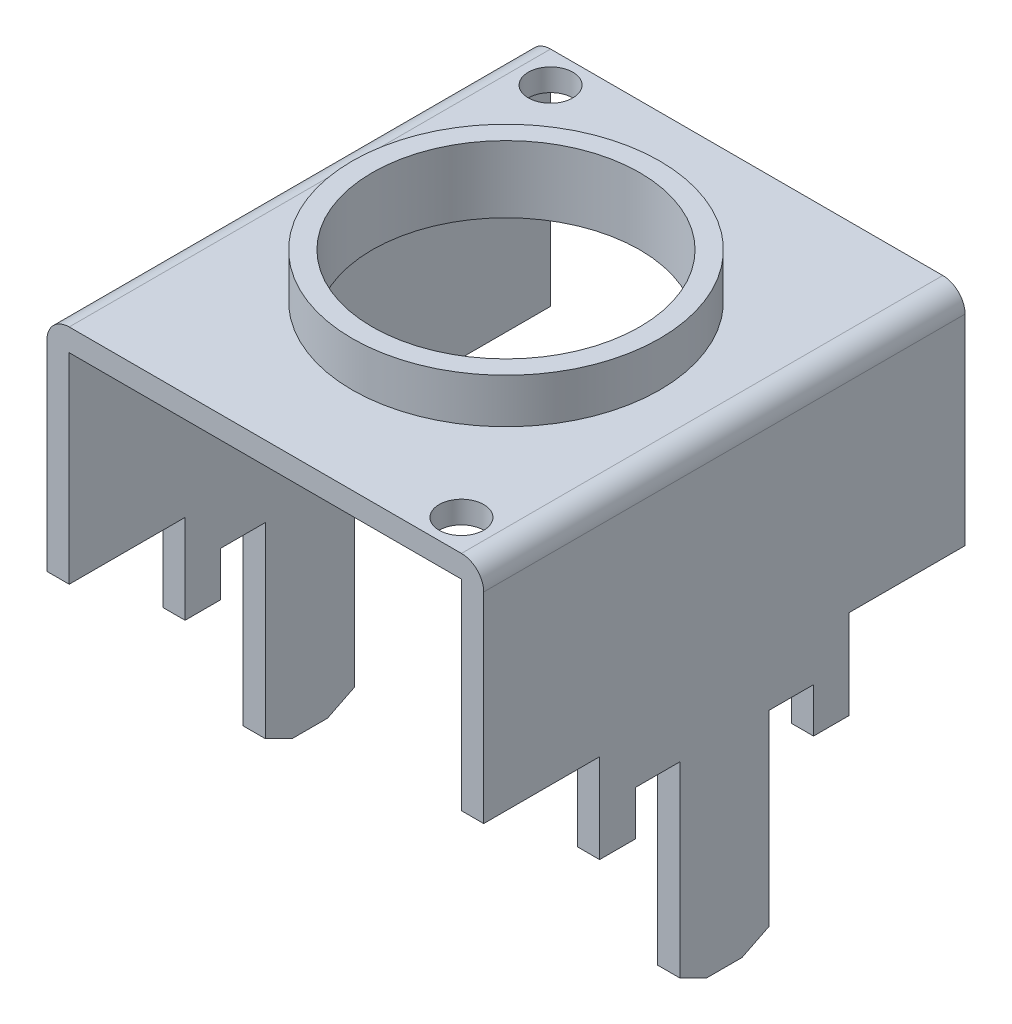
SolidWorks part; units mm, degrees
ref_plane "Plan de face" through (0, 0, 0) normal (0, 0, 1) x (1, 0, 0)
ref_plane "Plan de dessus" through (0, 0, 0) normal (0, 1, 0) x (1, 0, 0)
ref_plane "Plan de droite" through (0, 0, 0) normal (1, 0, 0) x (0, 0, -1)
sketch "Esquisse1" plane through (0, 0, 0) normal (0, 0, 1) x (1, 0, 0)
  line L0 (0, 5.7355) -> (0, -4.9955) construction
  line L1 (-4.9, -3.5) -> (-4.9, 6.5)
  line L2 (-4.4, 7) -> (4.4, 7)
  line L3 (4.9, 6.5) -> (4.9, -3.5)
  arc A0 (4.4, 7) -> (4.9, 6.5) centre (4.4, 6.5) cw
  arc A1 (-4.9, 6.5) -> (-4.4, 7) centre (-4.4, 6.5) cw
  dimension "D4" = 0.5
  dimension "D1" = 9.8
  dimension "D2" = 7
  dimension "D3" = 3.5
extrude "Extru.-Mince1" add sketch "Esquisse1" along normal blind 5.4 and the other way blind 5.4 thin
sketch "Esquisse3" plane through (0, 0, 0) normal (1, 0, 0) x (0, 0, -1)
  line L0 (0, 8.2867) -> (0, -5.5025) construction
  line L1 (-6.3578, 0) -> (5.9157, 0) construction
  line L2 (-6, 2) -> (-2.8, 2)
  line L3 (-2.8, 2) -> (-2.8, 0)
  line L4 (-2.8, 0) -> (-2, 0)
  line L5 (-2, 0) -> (-2, 1)
  line L6 (-2, 1) -> (-1, 1)
  line L7 (-1, 1) -> (-1, 0)
  line L8 (-1, 0) -> (-1, -3.2)
  line L9 (-1, -3.2) -> (-0.3953, -3.5)
  line L10 (5.4, -3.5) -> (-5.4, -3.5) construction
  line L11 (-0.3953, -3.5) -> (0.3953, -3.5)
  line L12 (-6, 2) -> (-6, -5)
  line L13 (-6, -5) -> (6, -5)
  line L14 (6, 2) -> (6, -5)
  line L15 (6, 2) -> (2.8, 2)
  line L16 (2.8, 2) -> (2.8, 0)
  line L17 (2.8, 0) -> (2, 0)
  line L18 (2, 0) -> (2, 1)
  line L19 (2, 1) -> (1, 1)
  line L20 (1, -3.2) -> (0.3953, -3.5)
  line L21 (1, 0) -> (1, -3.2)
  line L22 (1, 1) -> (1, 0)
  point P13 (0, 1.3921)
  point P14 (-2.8, 1)
  point P22 (0, -5)
  point P29 (0, -3.5)
  dimension "D1" = 2
  dimension "D2" = 1
  dimension "D3" = 2.8
  dimension "D4" = 1
  dimension "D5" = 0.3953
  dimension "D6" = 0.3
  dimension "D7" = 1
  dimension "D8" = 6
  dimension "D9" = 5
extrude "Enlèv. mat.-Extru.1" cut sketch "Esquisse3" against normal through all and the other way through all
sketch "Esquisse4" plane through (0, 7, 0) normal (0, 1, 0) x (1, 0, 0)
  line L0 (0, -6.0976) -> (0, 5.9322) construction
  line L1 (-5.5939, 0) -> (5.7292, 0) construction
  circle A0 centre (-3.7, 4.7) radius 0.5
  circle A1 centre (3.7, -4.7) radius 0.5
  dimension "D2" = 1
  dimension "D3" = 1
  dimension "D1" = 3.7
  dimension "D4" = 4.7
  dimension "D5" = 4.7
  dimension "D6" = 3.7
extrude "Enlèv. mat.-Extru.2" cut sketch "Esquisse4" against normal through all
sketch "Esquisse5" plane through (0, 7, 0) normal (0, 1, 0) x (1, 0, 0)
  circle A0 centre (0, 0) radius 3.45
  circle A1 centre (0, 0) radius 3
  dimension "D1" = 6.9
  dimension "D2" = 6
extrude "Boss.-Extru.1" add sketch "Esquisse5" along normal blind 1
sketch "Esquisse6" plane through (0, 7, 0) normal (0, 1, 0) x (1, 0, 0)
  circle A0 centre (0, 0) radius 3
  dimension "D1" = 6
extrude "Enlèv. mat.-Extru.3" cut sketch "Esquisse6" against normal through all
